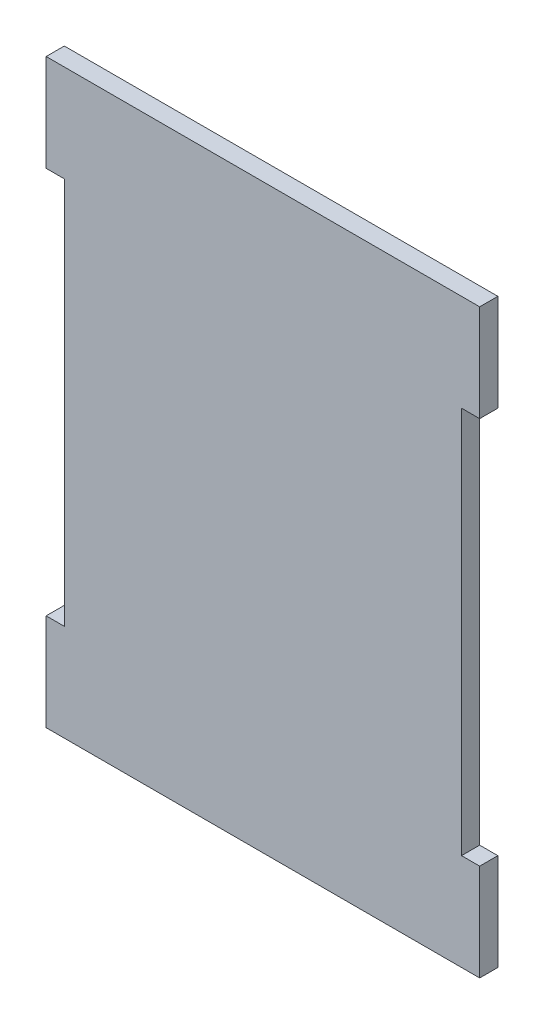
SolidWorks part; units mm, degrees
ref_plane "Front Plane" through (0, 0, 0) normal (0, 0, 1) x (1, 0, 0)
ref_plane "Top Plane" through (0, 0, 0) normal (0, 1, 0) x (1, 0, 0)
ref_plane "Right Plane" through (0, 0, 0) normal (1, 0, 0) x (0, 0, -1)
sketch "Sketch1" plane through (0, 0, 0) normal (0, 0, 1) x (1, 0, 0)
  line L0 (56.8325, 108.3954) -> (56.8325, -44.0046) construction
  line L1 (4.7625, 108.3954) -> (108.9025, 108.3954)
  line L2 (4.7625, 82.9954) -> (4.7625, -18.6046)
  line L3 (4.7625, -44.0046) -> (108.9025, -44.0046)
  line L5 (4.7625, 108.3954) -> (0, 108.3954)
  line L7 (4.7625, 82.9954) -> (0, 82.9954)
  line L8 (0, 108.3954) -> (0, 82.9954)
  line L9 (4.7625, 32.1954) -> (108.9025, 32.1954) construction
  line L10 (0, -44.0046) -> (0, -18.6046)
  line L11 (4.7625, -18.6046) -> (0, -18.6046)
  line L13 (4.7625, -44.0046) -> (0, -44.0046)
  line L14 (108.9025, -44.0046) -> (113.665, -44.0046)
  line L16 (108.9025, -18.6046) -> (113.665, -18.6046)
  line L17 (113.665, -44.0046) -> (113.665, -18.6046)
  line L18 (113.665, 108.3954) -> (113.665, 82.9954)
  line L19 (108.9025, 82.9954) -> (113.665, 82.9954)
  line L21 (108.9025, 108.3954) -> (113.665, 108.3954)
  line L22 (108.9025, 82.9954) -> (108.9025, -18.6046)
  dimension "D1" = 152.4
  dimension "D3" = 4.7625
  dimension "D4" = 25.4
extrude "Boss-Extrude1" add sketch "Sketch1" along normal blind 4.7625
